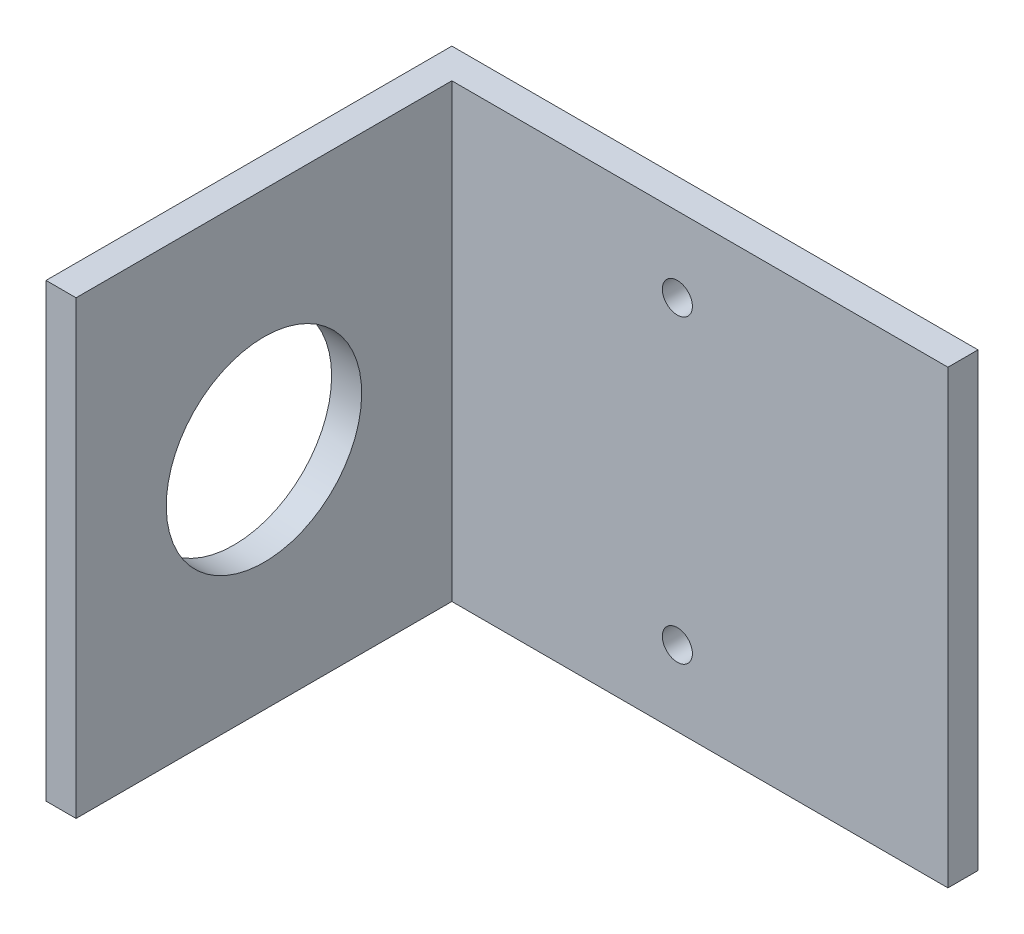
SolidWorks part; units mm, degrees
ref_plane "Front Plane" through (0, 0, 0) normal (0, 0, 1) x (1, 0, 0)
ref_plane "Top Plane" through (0, 0, 0) normal (0, 1, 0) x (1, 0, 0)
ref_plane "Right Plane" through (0, 0, 0) normal (1, 0, 0) x (0, 0, -1)
sketch "Sketch1" plane through (0, 0, 0) normal (0, 0, 1) x (1, 0, 0)
  line L1 (-35, 30) -> (35, 30)
  line L2 (-35, 30) -> (-35, -30)
  line L3 (-35, -30) -> (35, -30)
  line L4 (35, 30) -> (35, -30)
  line L5 (-35, 30) -> (35, -30) construction
  line L6 (-35, -30) -> (35, 30) construction
  point P0 (0, 0)
  dimension "D1" = 70
  dimension "D2" = 60
extrude "Boss-Extrude1" add sketch "Sketch1" along normal blind 4
sketch "Sketch2" plane through (0, 0, 4) normal (0, 0, 1) x (1, 0, 0)
  line L0 (-35, -30) -> (35, -30) construction
  line L1 (-35, 30) -> (-31, 30)
  line L2 (-35, 30) -> (-35, -30)
  line L3 (-35, -30) -> (-31, -30)
  line L4 (-31, 30) -> (-31, -30)
  dimension "D1" = 4
extrude "Boss-Extrude2" add sketch "Sketch2" along normal blind 50
sketch "Sketch3" plane through (-31, 0, 0) normal (1, 0, 0) x (0, 0, -1)
  circle A0 centre (-29, 0) radius 13
  dimension "D1" = 26
extrude "Cut-Extrude1" cut sketch "Sketch3" against normal blind 50
sketch "Sketch4" plane through (0, 0, 4) normal (0, 0, 1) x (1, 0, 0)
  line L0 (-31, 0) -> (-1, 0) construction
  line L1 (-31, -30) -> (-31, 30) construction
  line L2 (-1, 20) -> (-1, -20) construction
  circle A0 centre (-1, 20) radius 2
  circle A1 centre (-1, -20) radius 2
  point P8 (-1, 0)
  dimension "D3" = 4
  dimension "D4" = 4
  dimension "D1" = 30
  dimension "D2" = 40
extrude "Cut-Extrude2" cut sketch "Sketch4" against normal blind 50
